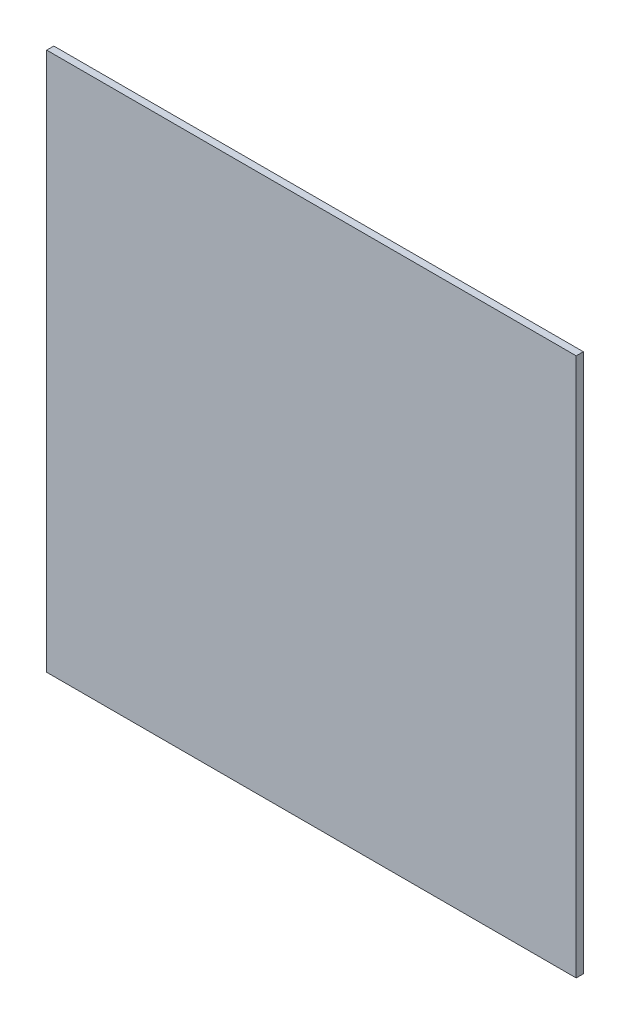
SolidWorks part; units mm, degrees
ref_plane "Front Plane" through (0, 0, 0) normal (0, 0, 1) x (1, 0, 0)
ref_plane "Top Plane" through (0, 0, 0) normal (0, 1, 0) x (1, 0, 0)
ref_plane "Right Plane" through (0, 0, 0) normal (1, 0, 0) x (0, 0, -1)
sketch "Sketch1" plane through (0, 0, 0) normal (0, 0, 1) x (1, 0, 0)
  line L1 (0, 0) -> (472.69, 0)
  line L2 (0, 0) -> (0, -481.0026)
  line L3 (0, -481.0026) -> (472.69, -481.0026)
  line L4 (472.69, 0) -> (472.69, -481.0026)
  dimension "D1" = 472.69
  dimension "D2" = 481.0026
extrude "Boss-Extrude1" add sketch "Sketch1" along normal blind 6.35
